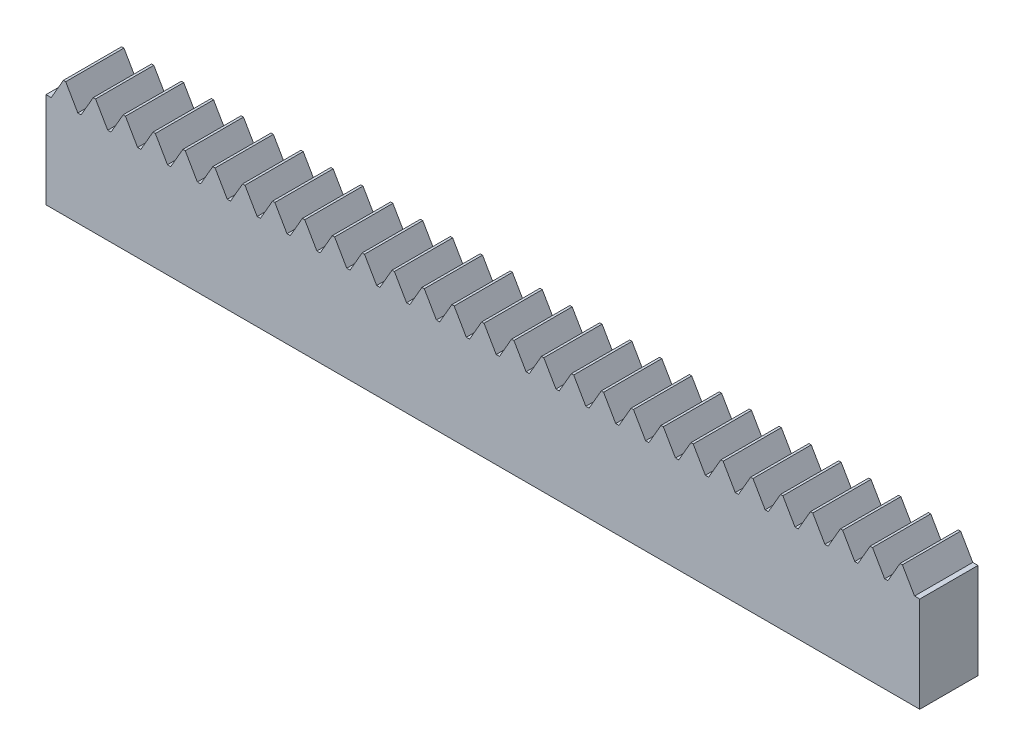
SolidWorks part; units mm, degrees
ref_plane "Front Plane" through (0, 0, 0) normal (0, 0, 1) x (1, 0, 0)
ref_plane "Top Plane" through (0, 0, 0) normal (0, 1, 0) x (1, 0, 0)
ref_plane "Right Plane" through (0, 0, 0) normal (1, 0, 0) x (0, 0, -1)
sketch "Sketch1" plane through (0, 0, 0) normal (0, 0, 1) x (1, 0, 0)
  line L0 (79.93, 0) -> (77.8458, -3.61)
  line L1 (2.98, 0) -> (3.38, 0)
  line L2 (0, -3.61) -> (0, -20)
  line L3 (0, -20) -> (150, -20)
  line L4 (150, -3.61) -> (150, -20)
  line L5 (5.4642, -3.61) -> (6.0258, -3.61)
  line L6 (0, -3.61) -> (0.8958, -3.61)
  line L7 (75, 0) -> (75.2, 0)
  line L8 (75.2, 0) -> (77.2842, -3.61)
  line L9 (74.8, 0) -> (72.7158, -3.61)
  line L10 (77.2842, -3.61) -> (77.8458, -3.61)
  line L11 (80.33, 0) -> (82.4142, -3.61)
  line L12 (85.06, 0) -> (82.9758, -3.61)
  line L13 (85.46, 0) -> (87.5442, -3.61)
  line L14 (90.19, 0) -> (88.1058, -3.61)
  line L15 (90.59, 0) -> (92.6742, -3.61)
  line L16 (95.32, 0) -> (93.2358, -3.61)
  line L17 (95.72, 0) -> (97.8042, -3.61)
  line L18 (100.45, 0) -> (98.3658, -3.61)
  line L19 (100.85, 0) -> (102.9342, -3.61)
  line L20 (105.58, 0) -> (103.4958, -3.61)
  line L21 (105.98, 0) -> (108.0642, -3.61)
  line L22 (110.71, 0) -> (108.6258, -3.61)
  line L23 (111.11, 0) -> (113.1942, -3.61)
  line L24 (115.84, 0) -> (113.7558, -3.61)
  line L25 (116.24, 0) -> (118.3242, -3.61)
  line L26 (120.97, 0) -> (118.8858, -3.61)
  line L27 (121.37, 0) -> (123.4542, -3.61)
  line L28 (126.1, 0) -> (124.0158, -3.61)
  line L29 (126.5, 0) -> (128.5842, -3.61)
  line L30 (131.23, 0) -> (129.1458, -3.61)
  line L31 (131.63, 0) -> (133.7142, -3.61)
  line L32 (136.36, 0) -> (134.2758, -3.61)
  line L33 (136.76, 0) -> (138.8442, -3.61)
  line L34 (141.49, 0) -> (139.4058, -3.61)
  line L35 (141.89, 0) -> (143.9742, -3.61)
  line L36 (146.62, 0) -> (144.5358, -3.61)
  line L37 (147.02, 0) -> (149.1042, -3.61)
  line L38 (70.07, 0) -> (72.1542, -3.61)
  line L39 (69.67, 0) -> (67.5858, -3.61)
  line L40 (64.94, 0) -> (67.0242, -3.61)
  line L41 (64.54, 0) -> (62.4558, -3.61)
  line L42 (59.81, 0) -> (61.8942, -3.61)
  line L43 (59.41, 0) -> (57.3258, -3.61)
  line L44 (54.68, 0) -> (56.7642, -3.61)
  line L45 (54.28, 0) -> (52.1958, -3.61)
  line L46 (49.55, 0) -> (51.6342, -3.61)
  line L47 (49.15, 0) -> (47.0658, -3.61)
  line L48 (150, -3.0311) -> (149.6658, -3.61) [skipped]
  line L49 (152.15, 0) -> (154.2342, -3.61) [skipped]
  line L50 (156.88, 0) -> (154.7958, -3.61) [skipped]
  line L51 (157.28, 0) -> (159.3642, -3.61) [skipped]
  line L52 (162.01, 0) -> (159.9258, -3.61) [skipped]
  line L53 (162.41, 0) -> (164.4942, -3.61) [skipped]
  line L54 (167.14, 0) -> (165.0558, -3.61) [skipped]
  line L55 (167.54, 0) -> (169.6242, -3.61) [skipped]
  line L56 (172.27, 0) -> (170.1858, -3.61) [skipped]
  line L57 (172.67, 0) -> (174.7542, -3.61) [skipped]
  line L58 (44.42, 0) -> (46.5042, -3.61)
  line L59 (44.02, 0) -> (41.9358, -3.61)
  line L60 (39.29, 0) -> (41.3742, -3.61)
  line L61 (38.89, 0) -> (36.8058, -3.61)
  line L62 (34.16, 0) -> (36.2442, -3.61)
  line L63 (33.76, 0) -> (31.6758, -3.61)
  line L64 (29.03, 0) -> (31.1142, -3.61)
  line L65 (28.63, 0) -> (26.5458, -3.61)
  line L66 (23.9, 0) -> (25.9842, -3.61)
  line L67 (23.5, 0) -> (21.4158, -3.61)
  line L68 (18.77, 0) -> (20.8542, -3.61)
  line L69 (18.37, 0) -> (16.2858, -3.61)
  line L70 (13.64, 0) -> (15.7242, -3.61)
  line L71 (13.24, 0) -> (11.1558, -3.61)
  line L72 (8.51, 0) -> (10.5942, -3.61)
  line L73 (8.11, 0) -> (6.0258, -3.61)
  line L74 (3.38, 0) -> (5.4642, -3.61)
  line L75 (2.98, 0) -> (0.8958, -3.61)
  line L76 (10.5942, -3.61) -> (11.1558, -3.61)
  line L77 (15.7242, -3.61) -> (16.2858, -3.61)
  line L78 (20.8542, -3.61) -> (21.4158, -3.61)
  line L79 (25.9842, -3.61) -> (26.5458, -3.61)
  line L80 (31.1142, -3.61) -> (31.6758, -3.61)
  line L81 (36.2442, -3.61) -> (36.8058, -3.61)
  line L82 (41.3742, -3.61) -> (41.9358, -3.61)
  line L83 (46.5042, -3.61) -> (47.0658, -3.61)
  line L84 (51.6342, -3.61) -> (52.1958, -3.61)
  line L85 (56.7642, -3.61) -> (57.3258, -3.61)
  line L86 (-2.15, 0) -> (-4.2342, -3.61) [skipped]
  line L87 (-6.88, 0) -> (-4.7958, -3.61) [skipped]
  line L88 (-7.28, 0) -> (-9.3642, -3.61) [skipped]
  line L89 (-12.01, 0) -> (-9.9258, -3.61) [skipped]
  line L90 (-12.41, 0) -> (-14.4942, -3.61) [skipped]
  line L91 (-17.14, 0) -> (-15.0558, -3.61) [skipped]
  line L92 (-17.54, 0) -> (-19.6242, -3.61) [skipped]
  line L93 (-22.27, 0) -> (-20.1858, -3.61) [skipped]
  line L94 (-22.67, 0) -> (-24.7542, -3.61) [skipped]
  line L95 (0, -3.0311) -> (0.3342, -3.61) [skipped]
  line L96 (61.8942, -3.61) -> (62.4558, -3.61)
  line L97 (67.0242, -3.61) -> (67.5858, -3.61)
  line L98 (72.1542, -3.61) -> (72.7158, -3.61)
  line L99 (82.4142, -3.61) -> (82.9758, -3.61)
  line L100 (87.5442, -3.61) -> (88.1058, -3.61)
  line L101 (92.6742, -3.61) -> (93.2358, -3.61)
  line L102 (97.8042, -3.61) -> (98.3658, -3.61)
  line L103 (102.9342, -3.61) -> (103.4958, -3.61)
  line L104 (108.0642, -3.61) -> (108.6258, -3.61)
  line L105 (113.1942, -3.61) -> (113.7558, -3.61)
  line L106 (118.3242, -3.61) -> (118.8858, -3.61)
  line L107 (123.4542, -3.61) -> (124.0158, -3.61)
  line L108 (128.5842, -3.61) -> (129.1458, -3.61)
  line L109 (133.7142, -3.61) -> (134.2758, -3.61)
  line L110 (138.8442, -3.61) -> (139.4058, -3.61)
  line L111 (143.9742, -3.61) -> (144.5358, -3.61)
  line L112 (149.1042, -3.61) -> (150, -3.61)
  line L113 (146.62, 0) -> (147.02, 0)
  line L114 (141.49, 0) -> (141.89, 0)
  line L115 (136.36, 0) -> (136.76, 0)
  line L116 (131.23, 0) -> (131.63, 0)
  line L117 (126.1, 0) -> (126.5, 0)
  line L118 (120.97, 0) -> (121.37, 0)
  line L119 (115.84, 0) -> (116.24, 0)
  line L120 (110.71, 0) -> (111.11, 0)
  line L121 (105.58, 0) -> (105.98, 0)
  line L122 (100.45, 0) -> (100.85, 0)
  line L123 (95.32, 0) -> (95.72, 0)
  line L124 (90.19, 0) -> (90.59, 0)
  line L125 (85.06, 0) -> (85.46, 0)
  line L126 (79.93, 0) -> (80.33, 0)
  line L127 (69.67, 0) -> (70.07, 0)
  line L128 (64.54, 0) -> (64.94, 0)
  line L129 (74.8, 0) -> (75.2, 0)
  line L130 (59.41, 0) -> (59.81, 0)
  line L131 (54.28, 0) -> (54.68, 0)
  line L132 (49.15, 0) -> (49.55, 0)
  line L133 (44.02, 0) -> (44.42, 0)
  line L134 (38.89, 0) -> (39.29, 0)
  line L135 (33.76, 0) -> (34.16, 0)
  line L136 (28.63, 0) -> (29.03, 0)
  line L137 (23.5, 0) -> (23.9, 0)
  line L138 (18.37, 0) -> (18.77, 0)
  line L139 (13.24, 0) -> (13.64, 0)
  line L140 (8.11, 0) -> (8.51, 0)
  dimension "D2" = 150
  dimension "D4" = 0.2
  dimension "D5" = 20
  dimension "D6" = 20
extrude "Boss-Extrude1" add sketch "Sketch1" along normal blind 10 contours L140 L73 L5 L74 L1 L75 L6 L2 L3 L4 L112 L37 L113 L36 L111 L35 L114 L34 L110 L33 L115 L32 L109 L31 L116 L30 L108 L29 L117 L28 L107 L27 L118 L26 L106 L25 L119 L24 L105 L23 L120 L22 L104 L21 L121 L20 L103 L19 L122 L18 L102
